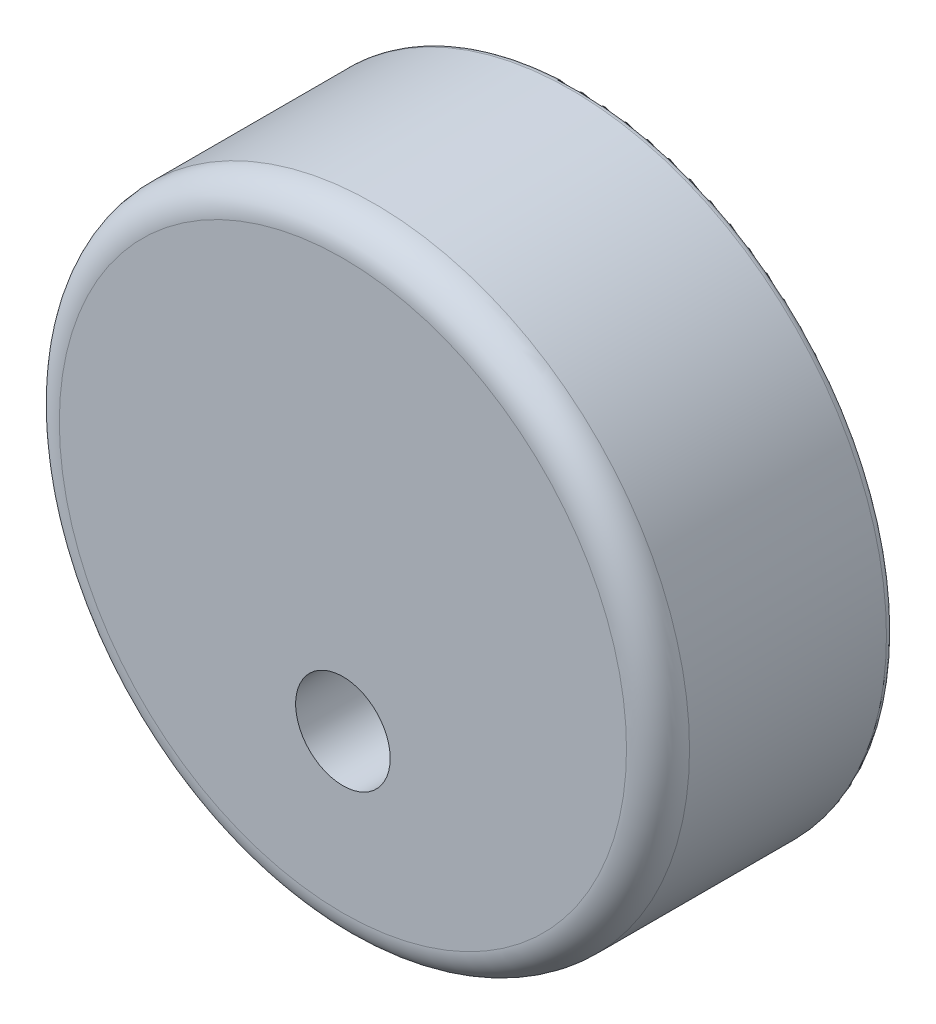
SolidWorks part; units mm, degrees
ref_plane "Front Plane" through (0, 0, 0) normal (0, 0, 1) x (1, 0, 0)
ref_plane "Top Plane" through (0, 0, 0) normal (0, 1, 0) x (1, 0, 0)
ref_plane "Right Plane" through (0, 0, 0) normal (1, 0, 0) x (0, 0, -1)
sketch "Sketch1" plane through (0, 0, 0) normal (0, 0, 1) x (1, 0, 0)
  circle A0 centre (0, 0) radius 20
  dimension "D1" = 40
extrude "Boss-Extrude1" add sketch "Sketch1" along normal blind 15
sketch "Sketch2" plane through (0, 0, 15) normal (0, 0, 1) x (1, 0, 0)
  circle A0 centre (0, -8) radius 3
  dimension "D1" = 6
  dimension "D2" = 8
extrude "Cut-Extrude1" cut sketch "Sketch2" against normal through all
fillet "Fillet1" radius 2 1 edges at (20, 0, 15)
fillet "Fillet2" radius 0.5 1 edges at (20, 0, 0)
sketch "Sketch3" plane through (0, 0, 0) normal (0, 0, -1) x (-1, 0, 0)
  line L0 (0, 22.0552) -> (0, -23.4244) construction
  line L1 (-27.0854, -8) -> (32.3834, -8) construction
  dimension "D1" = 8
